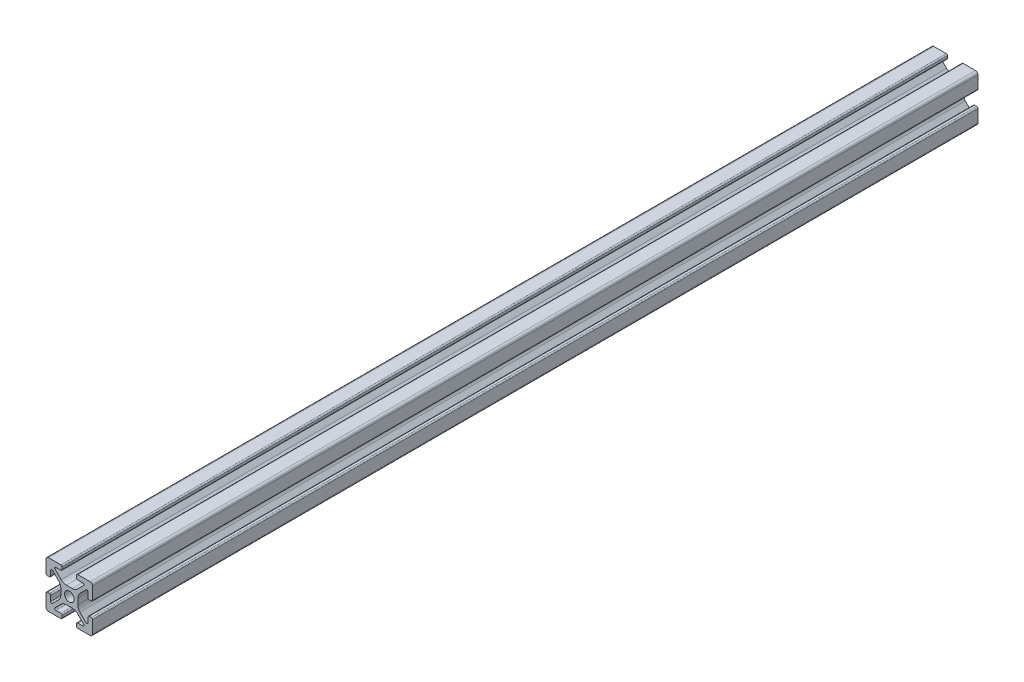
SolidWorks part; units mm, degrees
ref_plane "Front Plane" through (0, 0, 0) normal (0, 0, 1) x (1, 0, 0)
ref_plane "Top Plane" through (0, 0, 0) normal (0, 1, 0) x (1, 0, 0)
ref_plane "Right Plane" through (0, 0, 0) normal (1, 0, 0) x (0, 0, -1)
sketch "Sketch2" plane through (0, 0, 0) normal (0, 0, 1) x (1, 0, 0)
  line L0 (-3.6422, 1.2878) -> (-3.6422, -1.2878)
  line L1 (-1.2878, 3.6422) -> (1.2878, 3.6422)
  line L2 (-9.4433, 3.069) -> (-8.553, 3.069)
  line L3 (0, 0) -> (-15.7854, 0) construction
  line L4 (-3.4964, 4.5571) -> (-6.1213, 7.182)
  line L5 (-3.622, 8) -> (-5.7825, 8)
  line L6 (-3.069, 9.4433) -> (-3.069, 8.553)
  line L7 (-3.622, 10) -> (-8.939, 10)
  line L8 (0, 0) -> (0, 15.0393) construction
  line L9 (10, 3.622) -> (10, 8.939)
  line L10 (8, 3.622) -> (8, 5.7825)
  line L11 (4.5571, 3.4964) -> (7.182, 6.1213)
  line L12 (3.622, 10) -> (8.939, 10)
  line L13 (3.069, 9.4433) -> (3.069, 8.553)
  line L14 (3.622, 8) -> (5.7825, 8)
  line L15 (3.4964, 4.5571) -> (6.1213, 7.182)
  line L16 (9.4433, 3.069) -> (8.553, 3.069)
  line L17 (3.6422, 1.2878) -> (3.6422, -1.2878)
  line L18 (-10, -3.622) -> (-10, -8.939)
  line L19 (-8, -3.622) -> (-8, -5.7825)
  line L20 (-4.5571, -3.4964) -> (-7.182, -6.1213)
  line L21 (9.4433, -3.069) -> (8.553, -3.069)
  line L22 (3.4964, -4.5571) -> (6.1213, -7.182)
  line L23 (3.622, -8) -> (5.7825, -8)
  line L24 (3.069, -9.4433) -> (3.069, -8.553)
  line L25 (3.622, -10) -> (8.939, -10)
  line L26 (4.5571, -3.4964) -> (7.182, -6.1213)
  line L27 (8, -3.622) -> (8, -5.7825)
  line L28 (10, -3.622) -> (10, -8.939)
  line L29 (-3.622, -10) -> (-8.939, -10)
  line L30 (-3.069, -9.4433) -> (-3.069, -8.553)
  line L31 (-3.622, -8) -> (-5.7825, -8)
  line L32 (-3.4964, -4.5571) -> (-6.1213, -7.182)
  line L33 (-9.4433, -3.069) -> (-8.553, -3.069)
  line L34 (-1.2878, -3.6422) -> (1.2878, -3.6422)
  line L48 (-4.5571, 3.4964) -> (-7.182, 6.1213)
  line L49 (-8, 3.622) -> (-8, 5.7825)
  line L52 (-10, 3.622) -> (-10, 8.939)
  arc A0 (-8.553, 3.069) -> (-8, 3.622) centre (-8.553, 3.622) ccw
  arc A1 (-8, 5.7825) -> (-7.182, 6.1213) centre (-7.5208, 5.7825) cw
  arc A2 (-4.5571, 3.4964) -> (-3.6422, 1.2878) centre (-6.7657, 1.2878) cw
  arc A3 (-3.4964, 4.5571) -> (-1.2878, 3.6422) centre (-1.2878, 6.7657) ccw
  arc A4 (-5.7825, 8) -> (-6.1213, 7.182) centre (-5.7825, 7.5208) ccw
  arc A5 (-3.622, 10) -> (-3.069, 9.4433) centre (-3.622, 9.447) cw
  arc A6 (-3.069, 8.553) -> (-3.622, 8) centre (-3.622, 8.553) cw
  arc A7 (8.939, 10) -> (10, 8.939) centre (8.939, 8.939) cw
  arc A8 (10, 3.622) -> (9.4433, 3.069) centre (9.447, 3.622) cw
  arc A9 (3.069, 8.553) -> (3.622, 8) centre (3.622, 8.553) ccw
  arc A10 (3.622, 10) -> (3.069, 9.4433) centre (3.622, 9.447) ccw
  arc A11 (5.7825, 8) -> (6.1213, 7.182) centre (5.7825, 7.5208) cw
  arc A12 (3.4964, 4.5571) -> (1.2878, 3.6422) centre (1.2878, 6.7657) cw
  arc A13 (4.5571, 3.4964) -> (3.6422, 1.2878) centre (6.7657, 1.2878) ccw
  arc A14 (8, 5.7825) -> (7.182, 6.1213) centre (7.5208, 5.7825) ccw
  arc A15 (8.553, 3.069) -> (8, 3.622) centre (8.553, 3.622) cw
  arc A16 (-8.939, -10) -> (-10, -8.939) centre (-8.939, -8.939) cw
  arc A17 (-10, -3.622) -> (-9.4433, -3.069) centre (-9.447, -3.622) cw
  arc A18 (8.553, -3.069) -> (8, -3.622) centre (8.553, -3.622) ccw
  arc A19 (8, -5.7825) -> (7.182, -6.1213) centre (7.5208, -5.7825) cw
  arc A20 (4.5571, -3.4964) -> (3.6422, -1.2878) centre (6.7657, -1.2878) cw
  arc A21 (3.4964, -4.5571) -> (1.2878, -3.6422) centre (1.2878, -6.7657) ccw
  arc A22 (5.7825, -8) -> (6.1213, -7.182) centre (5.7825, -7.5208) ccw
  arc A23 (3.622, -10) -> (3.069, -9.4433) centre (3.622, -9.447) cw
  arc A24 (3.069, -8.553) -> (3.622, -8) centre (3.622, -8.553) cw
  arc A25 (10, -3.622) -> (9.4433, -3.069) centre (9.447, -3.622) ccw
  arc A26 (8.939, -10) -> (10, -8.939) centre (8.939, -8.939) ccw
  arc A27 (-3.069, -8.553) -> (-3.622, -8) centre (-3.622, -8.553) ccw
  arc A28 (-3.622, -10) -> (-3.069, -9.4433) centre (-3.622, -9.447) ccw
  arc A29 (-5.7825, -8) -> (-6.1213, -7.182) centre (-5.7825, -7.5208) cw
  arc A30 (-3.4964, -4.5571) -> (-1.2878, -3.6422) centre (-1.2878, -6.7657) cw
  arc A31 (-4.5571, -3.4964) -> (-3.6422, -1.2878) centre (-6.7657, -1.2878) ccw
  arc A32 (-8, -5.7825) -> (-7.182, -6.1213) centre (-7.5208, -5.7825) ccw
  arc A33 (-8.553, -3.069) -> (-8, -3.622) centre (-8.553, -3.622) cw
  arc A51 (-10, 3.622) -> (-9.4433, 3.069) centre (-9.447, 3.622) ccw
  arc A56 (-8.939, 10) -> (-10, 8.939) centre (-8.939, 8.939) ccw
  circle A57 centre (0, 0) radius 2.05
  point P1 (-3.6422, 0)
  point P46 (0, 0)
  point P48 (0, 0)
  point P53 (0, 3.6422)
  point P60 (0, 0)
  point P61 (0, 0)
  point P62 (0, 0)
  point P74 (0, 0)
  point P85 (0, 0)
  point P87 (0, 0)
  point P99 (0, 0)
  point P101 (0, 0)
  point P102 (0, 0)
  point P116 (0, -3.6422)
  point P117 (3.6422, 0)
  point P123 (0, 0)
  point P125 (0, 0)
  point P127 (0, 0)
  point P139 (0, 0)
  point P140 (0, 0)
  point P141 (0, 0)
  point P142 (0, 0)
  point P179 (0, 0)
  point P192 (0, 0)
  point P193 (0, 0)
  dimension "D1" = 0.553
  dimension "D3" = 3.1235
  dimension "D4" = 0.553
  dimension "D2" = 0.4792
  dimension "D5" = 1.061
  dimension "D6" = 2.05
extrude "Boss-Extrude1" add sketch "Sketch2" against normal blind 380
